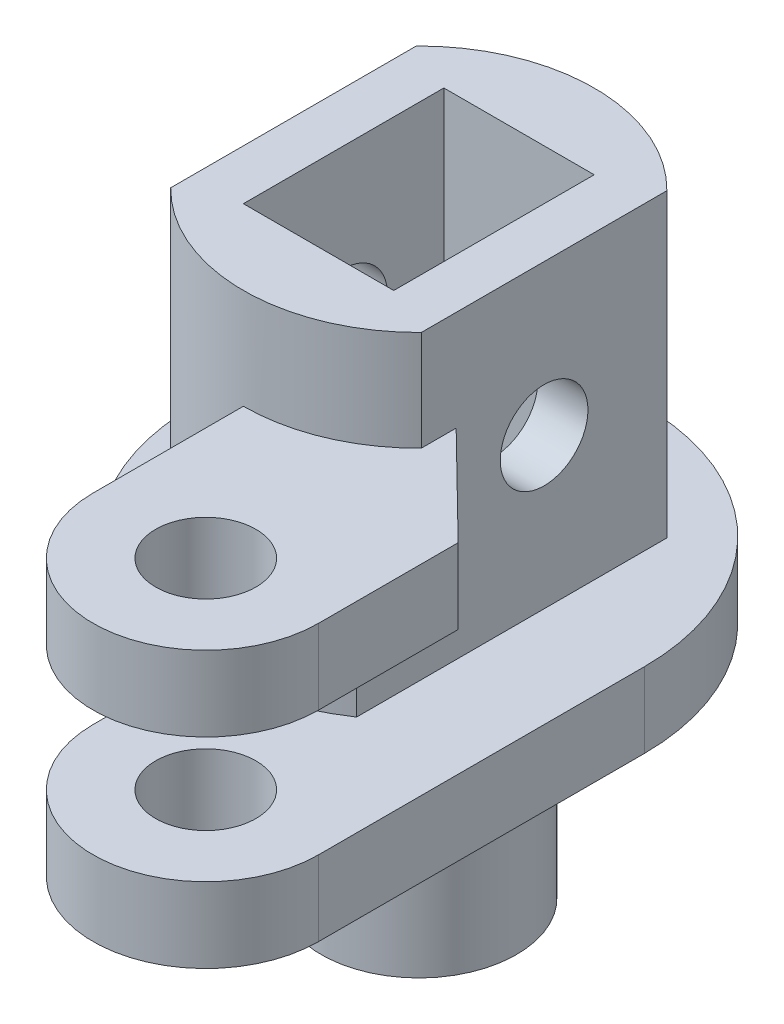
SolidWorks part; units mm, degrees
other "Markup1"
sketch "Sketch25" plane through (9, 15, 17.5) normal (0.6941, 0.3653, 0.6203) x (0.635, -0.7165, -0.2888)
ref_plane "Front Plane" through (0, 0, 0) normal (0, 0, 1) x (1, 0, 0)
ref_plane "Top Plane" through (0, 0, 0) normal (0, 1, 0) x (1, 0, 0)
ref_plane "Right Plane" through (0, 0, 0) normal (1, 0, 0) x (0, 0, -1)
sketch "Sketch1" plane through (0, 0, 0) normal (0, 1, 0) x (1, 0, 0)
  circle A0 centre (0, 0) radius 9
  dimension "D1" = 18
extrude "main body" add sketch "Sketch1" along normal blind 15
sketch "Sketch4" plane through (0, 0, 0) normal (0, -1, 0) x (1, 0, 0)
  circle A0 centre (0, 0) radius 6.4
  circle A1 centre (0, 0) radius 9 construction
  dimension "D1" = 12.8
extrude "Boss-Extrude3" add sketch "Sketch4" along normal blind 2.5 contours A0
sketch "Sketch5" plane through (0, -2.5, 0) normal (0, -1, 0) x (1, 0, 0)
  circle A0 centre (0, 0) radius 3.9
  circle A1 centre (0, 0) radius 6.4 construction
  dimension "D1" = 7.8
extrude "Boss-Extrude4" add sketch "Sketch5" along normal blind 7 contours A0
ref_plane "Plane1" through (0, 8, 0) normal (0, 1, 0) x (1, 0, 0)
sketch "Sketch9" plane through (0, 0, 0) normal (0, -1, 0) x (1, 0, 0)
  line L0 (0, 9) -> (0, 13)
  line L1 (9, 0) -> (9, 13)
  line L2 (0, 13) -> (9, 13) construction
  circle A0 centre (0, 0) radius 9 construction
  arc A2 (9, 0) -> (0, 9) centre (0, 0) ccw
  arc A3 (9, 13) -> (0, 13) centre (4.5, 13) ccw
  circle A4 centre (4.5, 13) radius 2
  dimension "D2" = 4.5
  dimension "D1" = 4
extrude "arm atttach" add sketch "Sketch9" against normal blind 3
ref_plane "Plane2" through (5, 0, 0) normal (1, 0, 0) x (0, 0, -1)
sketch "Sketch11" plane through (5, 0, 0) normal (1, 0, 0) x (0, 0, -1)
  line L0 (9, 0) -> (9, 15) construction
  line L1 (-9, 15) -> (9, 15)
  line L2 (-9, 15) -> (-9, 3)
  line L3 (-9, 3) -> (9, 3)
  line L4 (9, 15) -> (9, 3)
  dimension "D1" = 12
extrude "Cut-Extrude1" cut sketch "Sketch11" along normal blind 5
sketch "Sketch13" plane through (0, 8, 0) normal (0, 1, 0) x (1, 0, 0)
  line L0 (0, -13) -> (0, -9)
  line L1 (9, -13) -> (9, -7.4292)
  line L2 (9, -7.4292) -> (5, -3.5092)
  line L3 (5, -7.4833) -> (5, 7.4833) construction
  line L4 (5, -3.5092) -> (5, -7.4833)
  arc A0 (0, -13) -> (9, -13) centre (4.5, -13) ccw
  arc A1 (0, -9) -> (5, -7.4833) centre (0, 0) ccw
  circle A2 centre (4.5, -13) radius 2
extrude "arm attach" add sketch "Sketch13" along normal blind 3
ref_plane "Plane4" through (-5, 0, 0) normal (-1, 0, 0) x (0, 0, 1)
sketch "Sketch19" plane through (0, 15, 0) normal (0, 1, 0) x (1, 0, 0)
  line L0 (0, -7) -> (0, -9)
  line L1 (7.0839, -5.5514) -> (5.6441, -4.1405)
  line L2 (9, -7.4292) -> (5, -3.5092) construction
  arc A0 (5.6441, -4.1405) -> (0, -7) centre (0, 0) ccw
  arc A1 (7.0839, -5.5514) -> (0, -9) centre (0, 0) ccw
  dimension "D1" = 14
extrude "Cut-Extrude5" cut sketch "Sketch19" against normal up to surface (12 mm away) up to face at (4.8416, 3, 6.5616)
sketch "Sketch14" plane through (0, 15, 0) normal (0, 1, 0) x (1, 0, 0)
  line L1 (-3, 4) -> (3, 4)
  line L2 (-3, 4) -> (-3, -4)
  line L3 (-3, -4) -> (3, -4)
  line L4 (3, 4) -> (3, -4)
  line L5 (-3, 4) -> (3, -4) construction
  line L6 (-3, -4) -> (3, 4) construction
  point P0 (0, 0)
  dimension "D1" = 6
  dimension "D2" = 8
extrude "blade hole" cut sketch "Sketch14" against normal up to surface (12 mm away) up to face at (1.0369, 3, 5.4786)
sketch "Sketch21" plane through (-5, 0, 0) normal (-1, 0, 0) x (0, 0, 1)
  line L0 (-7, 9) -> (7, 9) construction
  line L1 (-7.5, 15) -> (7.5, 15)
  line L2 (-7.5, 15) -> (-7.5, 3)
  line L3 (-7.5, 3) -> (7.5, 3)
  line L4 (7.5, 15) -> (7.5, 3)
  line L5 (-7.5, 15) -> (7.5, 3) construction
  line L6 (-7.5, 3) -> (7.5, 15) construction
  line L7 (-7, 15) -> (-7, 3) construction
  line L8 (7, 3) -> (7, 15) construction
  point P0 (0, 9)
  dimension "D1" = 12
  dimension "D2" = 15
extrude "face cut" cut sketch "Sketch21" along normal blind 10
sketch "Sketch23" plane through (0, 15, 0) normal (0, 1, 0) x (1, 0, 0)
  circle A0 centre (0, 0) radius 7
  circle A1 centre (0, 0) radius 9
extrude "Cut-Extrude8" cut sketch "Sketch23" against normal up to surface (4 mm away) up to face at (4.6854, 11, 9.7154)
sketch "Sketch24" plane through (-5, 0, 0) normal (-1, 0, 0) x (0, 0, 1)
  line L0 (0, 15) -> (0, 3) construction
  line L1 (4.899, 15) -> (-4.899, 15) construction
  line L2 (9, 3) -> (-9, 3) construction
  circle A0 centre (0, 9) radius 1.75
  dimension "D1" = 3.5
extrude "screw hole" cut sketch "Sketch24" against normal mid plane 30
sketch "Sketch26" plane through (0, 0, 0) normal (0, 1, 0) x (1, 0, 0)
  circle A0 centre (0, 0) radius 1.65
  dimension "D1" = 3.3
extrude "Cut-Extrude9" cut sketch "Sketch26" against normal through all both and the other way through all
